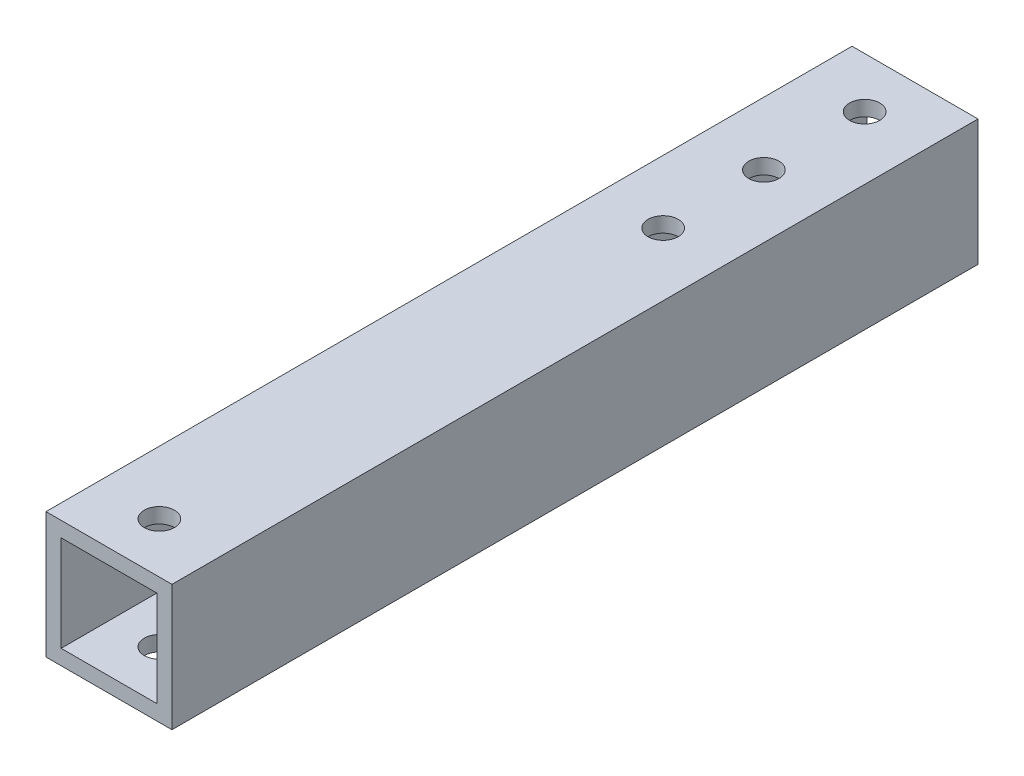
SolidWorks part; units mm, degrees
ref_plane "Front Plane" through (0, 0, 0) normal (0, 0, 1) x (1, 0, 0)
ref_plane "Top Plane" through (0, 0, 0) normal (0, 1, 0) x (1, 0, 0)
ref_plane "Right Plane" through (0, 0, 0) normal (1, 0, 0) x (0, 0, -1)
sketch "Sketch1" plane through (0, 0, 0) normal (0, 0, 1) x (1, 0, 0)
  line L0 (3, 22) -> (22, 22)
  line L1 (0, 0) -> (25, 0)
  line L2 (0, 0) -> (0, 25)
  line L3 (0, 25) -> (25, 25)
  line L4 (25, 0) -> (25, 25)
  line L5 (22, 3) -> (22, 22)
  line L6 (3, 3) -> (22, 3)
  line L7 (3, 3) -> (3, 22)
  dimension "D1" = 25
  dimension "D2" = 3
extrude "Boss-Extrude1" add sketch "Sketch1" along normal blind 160
sketch "Sketch2" plane through (0, 0, 0) normal (0, -1, 0) x (1, 0, 0)
  line L0 (12.5, 160) -> (12.5, 0) construction
  line L1 (0, 160) -> (25, 160) construction
  line L2 (0, 0) -> (25, 0) construction
  circle A0 centre (12.5, 10) radius 3
  circle A1 centre (12.5, 30) radius 3
  circle A2 centre (12.5, 50) radius 3
  circle A3 centre (12.5, 150) radius 3
  dimension "D5" = 6
  dimension "D1" = 10
  dimension "D2" = 20
  dimension "D3" = 20
  dimension "D4" = 10
extrude "Cut-Extrude1" cut sketch "Sketch2" against normal through all
